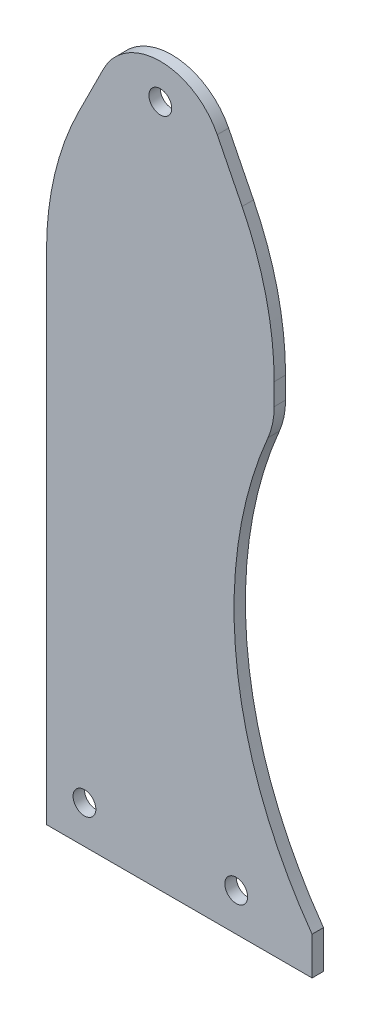
SolidWorks part; units mm, degrees
material "普通碳钢"
ref_plane "前视基准面" through (0, 0, 0) normal (0, 0, 1) x (1, 0, 0)
ref_plane "上视基准面" through (0, 0, 0) normal (0, 1, 0) x (1, 0, 0)
ref_plane "右视基准面" through (0, 0, 0) normal (1, 0, 0) x (0, 0, -1)
sketch "草图1" plane through (0, 0, 0) normal (0, 0, 1) x (1, 0, 0)
  line L0 (8.4458, 166.8916) -> (15, 180)
  line L1 (30, 180) -> (30, 0) construction
  line L2 (15, 180) -> (45, 180) construction
  line L3 (0, 131.1146) -> (0, 10)
  line L4 (0, 0) -> (60, 0)
  line L5 (60, 131.1146) -> (60, 125.4124)
  line L6 (51.5542, 166.8916) -> (45, 180)
  line L7 (60, 0) -> (70, 0)
  line L8 (70, 0) -> (70, 10)
  line L9 (0, 10) -> (0, 0)
  arc A0 (60, 131.1146) -> (51.5542, 166.8916) centre (-20, 131.1146) ccw
  arc A1 (0, 131.1146) -> (8.4458, 166.8916) centre (80, 131.1146) cw
  arc A2 (15, 180) -> (45, 180) centre (30, 172.5) cw
  arc A3 (70, 10) -> (58.3732, 117.5113) centre (159.4255, 74.0553) cw
  arc A4 (58.3732, 117.5113) -> (60, 125.4124) centre (40, 125.4124) ccw
  circle A5 centre (10, 10) radius 3
  circle A6 centre (50, 10) radius 3
  circle A7 centre (30, 180) radius 3
  point P13 (60, 150)
  point P16 (0, 150)
  point P22 (60, 121.1146)
  dimension "D5" = 80
  dimension "D6" = 80
  dimension "D7" = 10
  dimension "D8" = 10
  dimension "D10" = 110
  dimension "D11" = 20
  dimension "D12" = 6
  dimension "D15" = 6
  dimension "D1" = 30
  dimension "D2" = 60
  dimension "D3" = 15
  dimension "D4" = 180
  dimension "D9" = 10
  dimension "D13" = 10
  dimension "D14" = 10
  dimension "D16" = 0
extrude "凸台-拉伸1" add sketch "草图1" along normal blind 3
